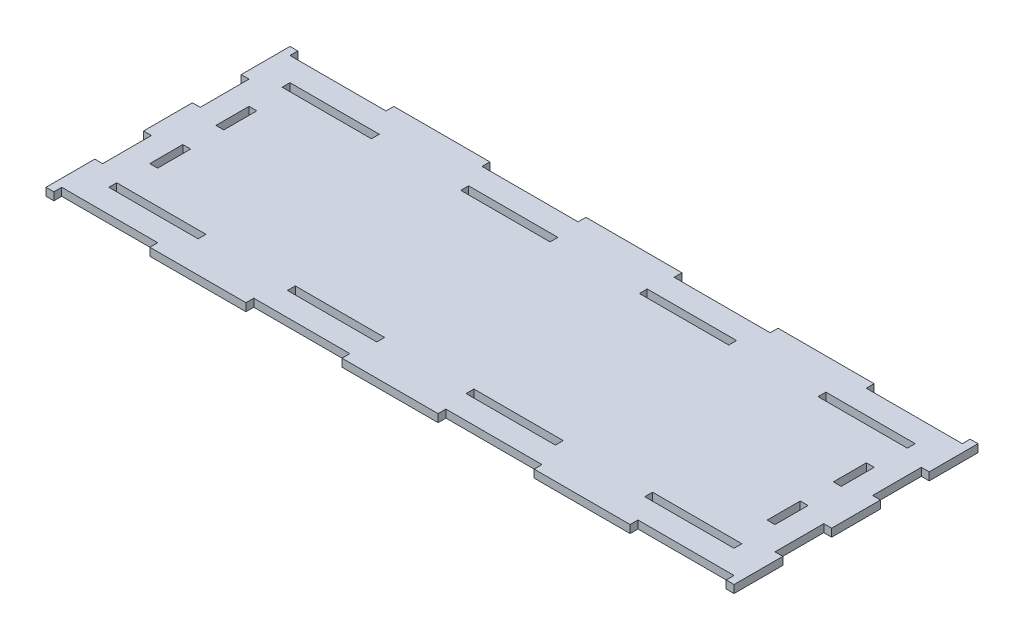
SolidWorks part; units mm, degrees
ref_plane "Front Plane" through (0, 0, 0) normal (0, 0, 1) x (1, 0, 0)
ref_plane "Top Plane" through (0, 0, 0) normal (0, 1, 0) x (1, 0, 0)
ref_plane "Right Plane" through (0, 0, 0) normal (1, 0, 0) x (0, 0, -1)
sketch "Sketch1" plane through (0, 0, 0) normal (0, 1, 0) x (1, 0, 0)
  line L1 (-233, -63.25) -> (233, -63.25)
  line L2 (-233, -63.25) -> (-233, 63.25)
  line L3 (-233, 63.25) -> (233, 63.25)
  line L4 (233, -63.25) -> (233, 63.25)
  line L5 (-233, -63.25) -> (233, 63.25) construction
  line L6 (-233, 63.25) -> (233, -63.25) construction
  point P0 (0, 0)
  dimension "D1" = 126.5
  dimension "D2" = 466
extrude "Boss-Extrude1" add sketch "Sketch1" along normal blind 6
sketch "Sketch2" plane through (0, 6, 0) normal (0, 1, 0) x (1, 0, 0)
  line L0 (239, -69.25) -> (239, 69.25)
  line L3 (-239, -69.25) -> (239, -69.25)
  line L4 (233, -63.25) -> (233, 63.25)
  line L5 (233, 63.25) -> (-233, 63.25)
  line L6 (-233, 63.25) -> (-233, -63.25)
  line L7 (-233, -63.25) -> (233, -63.25)
  line L8 (233, -63.25) -> (233, 63.25)
  line L9 (233, 63.25) -> (-233, 63.25)
  line L10 (-233, 63.25) -> (-233, -63.25)
  line L11 (-233, -63.25) -> (233, -63.25)
  line L12 (257, -87.25) -> (257, 87.25)
  line L13 (257, 87.25) -> (-257, 87.25)
  line L14 (-257, 87.25) -> (-257, -87.25)
  line L15 (-257, -87.25) -> (257, -87.25)
  line L16 (263, -93.25) -> (263, 93.25)
  line L19 (-263, -93.25) -> (263, -93.25)
  line L20 (239, 69.25) -> (-239, 69.25) construction
  line L21 (-239, 69.25) -> (-239, -69.25) construction
  line L22 (-239, -69.25) -> (-239, -63.25)
  line L27 (170.7143, 69.25) -> (102.4286, 69.25)
  line L28 (170.7143, 69.25) -> (170.7143, 63.25)
  line L29 (170.7143, 63.25) -> (102.4286, 63.25)
  line L30 (102.4286, 69.25) -> (102.4286, 63.25)
  line L31 (102.4286, 69.25) -> (34.1429, 69.25)
  line L32 (102.4286, 69.25) -> (102.4286, 63.25)
  line L33 (102.4286, 63.25) -> (34.1429, 63.25)
  line L34 (34.1429, 69.25) -> (34.1429, 63.25)
  line L35 (34.1429, 69.25) -> (-34.1429, 69.25)
  line L36 (34.1429, 69.25) -> (34.1429, 63.25)
  line L37 (34.1429, 63.25) -> (-34.1429, 63.25)
  line L38 (-34.1429, 69.25) -> (-34.1429, 63.25)
  line L39 (-34.1429, 69.25) -> (-102.4286, 69.25)
  line L40 (-34.1429, 69.25) -> (-34.1429, 63.25)
  line L41 (-34.1429, 63.25) -> (-102.4286, 63.25)
  line L42 (-102.4286, 69.25) -> (-102.4286, 63.25)
  line L43 (-102.4286, 69.25) -> (-170.7143, 69.25)
  line L44 (-102.4286, 69.25) -> (-102.4286, 63.25)
  line L45 (-102.4286, 63.25) -> (-170.7143, 63.25)
  line L46 (-170.7143, 69.25) -> (-170.7143, 63.25)
  line L47 (-170.7143, 69.25) -> (-239, 69.25)
  line L48 (-170.7143, 69.25) -> (-170.7143, 63.25)
  line L49 (-170.7143, 63.25) -> (-239, 63.25)
  line L50 (-239, 69.25) -> (-239, 63.25)
  line L51 (-239, 63.25) -> (-233, 63.25)
  line L52 (-239, 63.25) -> (-239, 37.95)
  line L53 (-239, 37.95) -> (-233, 37.95)
  line L54 (-233, 63.25) -> (-233, 37.95)
  line L55 (-233, 37.95) -> (-239, 37.95)
  line L56 (-233, 37.95) -> (-233, 12.65)
  line L57 (-233, 12.65) -> (-239, 12.65)
  line L58 (-239, 37.95) -> (-239, 12.65)
  line L59 (-239, 12.65) -> (-233, 12.65)
  line L60 (-239, 12.65) -> (-239, -12.65)
  line L61 (-239, -12.65) -> (-233, -12.65)
  line L62 (-233, 12.65) -> (-233, -12.65)
  line L63 (-233, -12.65) -> (-239, -12.65)
  line L64 (-233, -12.65) -> (-233, -37.95)
  line L65 (-233, -37.95) -> (-239, -37.95)
  line L66 (-239, -12.65) -> (-239, -37.95)
  line L67 (-239, -37.95) -> (-233, -37.95)
  line L68 (-239, -37.95) -> (-239, -63.25)
  line L69 (-239, -63.25) -> (-233, -63.25)
  line L70 (-233, -37.95) -> (-233, -63.25)
  line L71 (170.7143, 63.25) -> (239, 63.25)
  line L72 (170.7143, 63.25) -> (170.7143, 69.25)
  line L73 (170.7143, 69.25) -> (239, 69.25)
  line L74 (239, 63.25) -> (239, 69.25)
  line L75 (-263, 93.25) -> (-257, 93.25)
  line L76 (-263, 93.25) -> (-263, 55.95)
  line L77 (-263, 55.95) -> (-257, 55.95)
  line L78 (-257, 93.25) -> (-257, 55.95)
  line L79 (-263, 93.25) -> (-263, -93.25) construction
  line L80 (-257, 55.95) -> (-263, 55.95)
  line L81 (-257, 55.95) -> (-257, 18.65)
  line L82 (-257, 18.65) -> (-263, 18.65)
  line L83 (-263, 55.95) -> (-263, 18.65)
  line L84 (-263, 18.65) -> (-257, 18.65)
  line L85 (-263, 18.65) -> (-263, -18.65)
  line L86 (-263, -18.65) -> (-257, -18.65)
  line L87 (-257, 18.65) -> (-257, -18.65)
  line L88 (-257, -18.65) -> (-263, -18.65)
  line L89 (-257, -18.65) -> (-257, -55.95)
  line L90 (-257, -55.95) -> (-263, -55.95)
  line L91 (-263, -18.65) -> (-263, -55.95)
  line L92 (-263, -55.95) -> (-257, -55.95)
  line L93 (-263, -55.95) -> (-263, -93.25)
  line L94 (-263, -93.25) -> (-257, -93.25)
  line L95 (-257, -55.95) -> (-257, -93.25)
  line L96 (257, 87.25) -> (183.5714, 87.25)
  line L97 (257, 87.25) -> (257, 93.25)
  line L98 (257, 93.25) -> (183.5714, 93.25)
  line L99 (183.5714, 87.25) -> (183.5714, 93.25)
  line L100 (183.5714, 93.25) -> (110.1429, 93.25)
  line L101 (183.5714, 93.25) -> (183.5714, 87.25)
  line L102 (183.5714, 87.25) -> (110.1429, 87.25)
  line L103 (110.1429, 93.25) -> (110.1429, 87.25)
  line L104 (110.1429, 87.25) -> (36.7143, 87.25)
  line L105 (110.1429, 87.25) -> (110.1429, 93.25)
  line L106 (110.1429, 93.25) -> (36.7143, 93.25)
  line L107 (36.7143, 87.25) -> (36.7143, 93.25)
  line L108 (36.7143, 93.25) -> (-36.7143, 93.25)
  line L109 (36.7143, 93.25) -> (36.7143, 87.25)
  line L110 (36.7143, 87.25) -> (-36.7143, 87.25)
  line L111 (-36.7143, 93.25) -> (-36.7143, 87.25)
  line L112 (-36.7143, 87.25) -> (-110.1429, 87.25)
  line L113 (-36.7143, 87.25) -> (-36.7143, 93.25)
  line L114 (-36.7143, 93.25) -> (-110.1429, 93.25)
  line L115 (-110.1429, 87.25) -> (-110.1429, 93.25)
  line L116 (-110.1429, 93.25) -> (-183.5714, 93.25)
  line L117 (-110.1429, 93.25) -> (-110.1429, 87.25)
  line L118 (-110.1429, 87.25) -> (-183.5714, 87.25)
  line L119 (-183.5714, 93.25) -> (-183.5714, 87.25)
  line L120 (-183.5714, 87.25) -> (-257, 87.25)
  line L121 (-183.5714, 87.25) -> (-183.5714, 93.25)
  line L122 (-183.5714, 93.25) -> (-257, 93.25)
  line L123 (-257, 87.25) -> (-257, 93.25)
  line L124 (263, 93.25) -> (-263, 93.25) construction
  line L125 (263, 93.25) -> (257, 93.25)
  line M94 (-233, 63.25) -> (-233, -63.25)
  dimension "D1" = 0
  dimension "D2" = 6
  dimension "D3" = 18
  dimension "D4" = 6
extrude "Boss-Extrude2" add sketch "Sketch2" against normal blind 6 contours L27 L30 L9 L28 | L43 L46 L9 L42 | L35 L38 L9 L34 | L14 L15 L12 L13 L27 L73 L0 L3 L22 L68 L66 L60 L58 L52 L50 L47 L43 L39 L35 L31 | L116 L119 L13 L115 | L108 L111 L13 L107 | L100 L103 L13 L99 | L52 L53 L49 M94 | L78 L75 L76 L77 L14 | L60 L61 L57 M94 | L85 L86 L14 L82 | L68 L69 L65 M94 | L95 L14 L90 L93 L19
mirror "Mirror2" about plane through (0, 0, 0) normal (0, 0, 1) of "Boss-Extrude2"
mirror "Mirror3" about plane through (0, 0, 0) normal (1, 0, 0) of "Boss-Extrude2"
